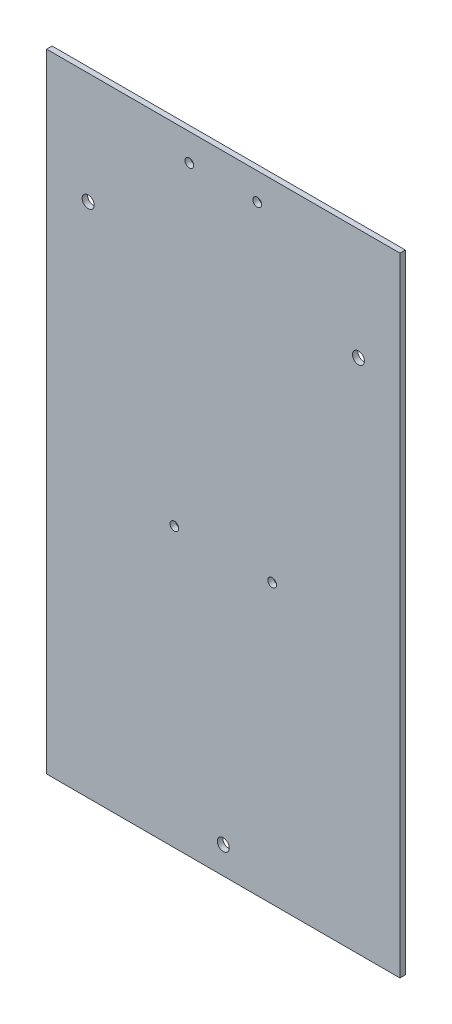
SolidWorks part; units mm, degrees
material "ｱｸﾘﾙ (中-上級の耐衝撃性)"
ref_plane "正面" through (0, 0, 0) normal (0, 0, 1) x (1, 0, 0)
ref_plane "平面" through (0, 0, 0) normal (0, 1, 0) x (1, 0, 0)
ref_plane "右側面" through (0, 0, 0) normal (1, 0, 0) x (0, 0, -1)
sketch "ｽｹｯﾁ1" plane through (0, 0, 0) normal (0, 0, 1) x (1, 0, 0)
  line L1 (-75, 115.5) -> (75, 115.5)
  line L2 (-75, 115.5) -> (-75, -115.5)
  line L3 (-75, -115.5) -> (75, -115.5)
  line L4 (75, 115.5) -> (75, -115.5)
  line L5 (-75, 115.5) -> (75, -115.5) construction
  line L6 (-75, -115.5) -> (75, 115.5) construction
  point P0 (0, 0)
  dimension "D1" = 150
  dimension "D2" = 231
extrude "ﾎﾞｽ - 押し出し1" add sketch "ｽｹｯﾁ1" along normal blind 2
sketch "ｽｹｯﾁ2" plane through (0, 0, 2) normal (0, 0, 1) x (1, 0, 0)
  line L0 (0, 115.5) -> (0, 74.5)
  line L1 (75, 115.5) -> (-75, 115.5) construction
  line L2 (0, 74.5) -> (49.73, 74.5)
  line L3 (0, 74.5) -> (-49.73, 74.5)
  line L4 (0, 74.5) -> (0, -105.5)
  circle A0 centre (49.73, 74.5) radius 2.2
  circle A1 centre (-49.73, 74.5) radius 2.2
  circle A2 centre (0, -105.5) radius 2.2
  dimension "D5" = 4.4
  dimension "D6" = 4.4
  dimension "D7" = 4.4
  dimension "D1" = 41
  dimension "D2" = 49.73
  dimension "D3" = 49.73
  dimension "D4" = 180
extrude "ｶｯﾄ - 押し出し1" cut sketch "ｽｹｯﾁ2" against normal blind 2
sketch "ｽｹｯﾁ3" plane through (0, 0, 2) normal (0, 0, 1) x (1, 0, 0)
  line L0 (0, 0) -> (0, -13)
  line L1 (0, 74.5) -> (0, -105.5) construction
  line L2 (0, -13) -> (18, -13)
  line L3 (0, -13) -> (-18, -13)
  circle A0 centre (-18, -13) radius 1.6
  circle A1 centre (18, -13) radius 1.6
  dimension "D4" = 3.2
  dimension "D5" = 3.2
  dimension "D1" = 13
  dimension "D2" = 18
  dimension "D3" = 18
extrude "ｶｯﾄ - 押し出し2" cut sketch "ｽｹｯﾁ3" against normal blind 10
sketch "ｽｹｯﾁ4" plane through (-75, 0, 0) normal (-1, 0, 0) x (0, 0, 1)
  line L1 (0, -115.5) -> (2, -115.5)
  line L2 (0, -115.5) -> (0, 115.5)
  line L3 (0, 115.5) -> (2, 115.5)
  line L4 (2, -115.5) -> (2, 115.5)
extrude "ｶｯﾄ - 押し出し3" cut sketch "ｽｹｯﾁ4" against normal blind 10
sketch "ｽｹｯﾁ5" plane through (75, 0, 0) normal (1, 0, 0) x (0, 0, -1)
  line L1 (-2, 115.5) -> (0, 115.5)
  line L2 (-2, 115.5) -> (-2, -115.5)
  line L3 (-2, -115.5) -> (0, -115.5)
  line L4 (0, 115.5) -> (0, -115.5)
extrude "ｶｯﾄ - 押し出し4" cut sketch "ｽｹｯﾁ5" against normal blind 10
sketch "ｽｹｯﾁ6" plane through (0, 0, 0) normal (0, 0, -1) x (-1, 0, 0)
  line L0 (0, 115.5) -> (0, 105.5)
  line L1 (0, 115.5) -> (0, 74.5) construction
  line L2 (0, 105.5) -> (12.5, 105.5)
  line L3 (0, 105.5) -> (-12.5, 105.5)
  circle A0 centre (-12.5, 105.5) radius 1.6
  circle A1 centre (12.5, 105.5) radius 1.6
  point P9 (0, 0)
  dimension "D2" = 3.2
  dimension "D3" = 3.2
  dimension "D1" = 10
  dimension "D4" = 12.5
  dimension "D5" = 12.5
extrude "ｶｯﾄ - 押し出し5" cut sketch "ｽｹｯﾁ6" against normal blind 10
